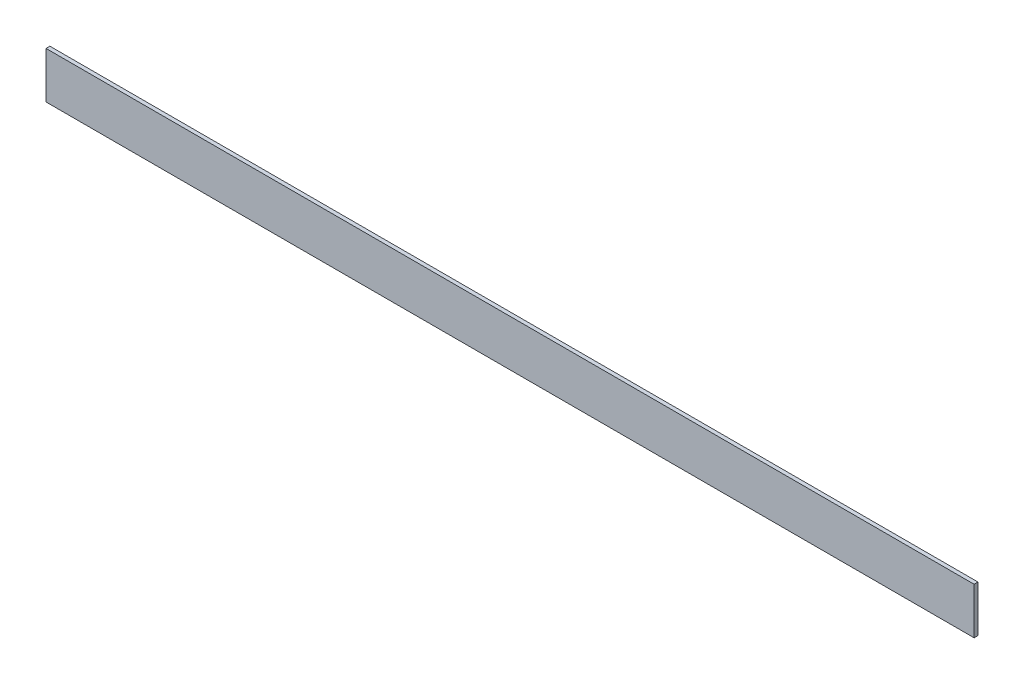
SolidWorks part; units mm, degrees
material "PVC 0.007 Plasticized"
ref_plane "Front Plane" through (0, 0, 0) normal (0, 0, 1) x (1, 0, 0)
ref_plane "Top Plane" through (0, 0, 0) normal (0, 1, 0) x (1, 0, 0)
ref_plane "Right Plane" through (0, 0, 0) normal (1, 0, 0) x (0, 0, -1)
sketch "Sketch1" plane through (0, 0, 0) normal (1, 0, 0) x (0, 0, -1)
  line L1 (-3.175, -38.1) -> (3.175, -38.1)
  line L2 (-3.175, -38.1) -> (-3.175, 38.1)
  line L3 (-3.175, 38.1) -> (3.175, 38.1)
  line L4 (3.175, -38.1) -> (3.175, 38.1)
  line L5 (-3.175, -38.1) -> (3.175, 38.1) construction
  line L6 (-3.175, 38.1) -> (3.175, -38.1) construction
  point P0 (0, 0)
  dimension "D1" = 76.2
  dimension "D2" = 6.35
extrude "Boss-Extrude1" add sketch "Sketch1" along normal blind 1524
equation "\"D2@Sketch1\"=1in/4"
